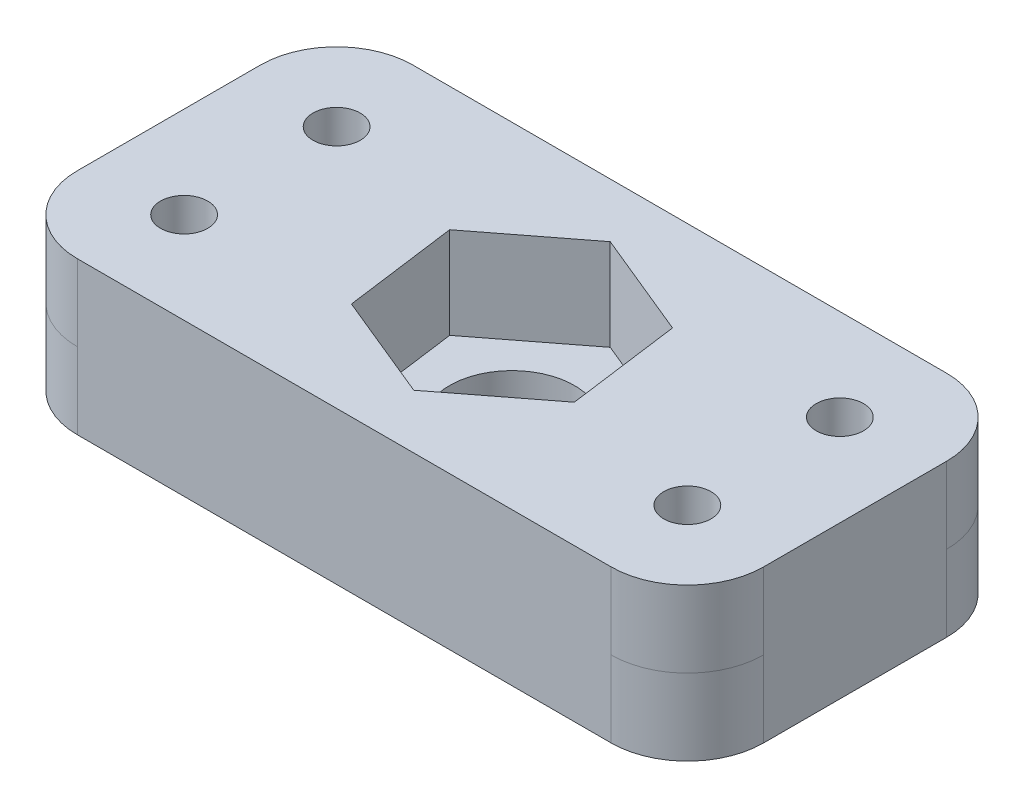
SolidWorks part; units mm, degrees
ref_plane "Alzado" through (0, 0, 0) normal (0, 0, 1) x (1, 0, 0)
ref_plane "Planta" through (0, 0, 0) normal (0, 1, 0) x (1, 0, 0)
ref_plane "Vista lateral" through (0, 0, 0) normal (1, 0, 0) x (0, 0, -1)
sketch "Croquis1" plane through (0, 0, 0) normal (0, 1, 0) x (1, 0, 0)
  circle A0 centre (0, 0) radius 10
  circle A1 centre (0, 0) radius 3.5
  dimension "D1" = 20
  dimension "D2" = 7
extrude "Extruir1" add sketch "Croquis1" along normal blind 12
sketch "Croquis2" plane through (0, 12, 0) normal (0, 1, 0) x (1, 0, 0)
  line L1 (22.5, 11) -> (-22.5, 11)
  line L2 (22.5, 11) -> (22.5, -11)
  line L3 (22.5, -11) -> (-22.5, -11)
  line L4 (-22.5, 11) -> (-22.5, -11)
  line L5 (22.5, 11) -> (-22.5, -11) construction
  line L6 (22.5, -11) -> (-22.5, 11) construction
  point P0 (0, 0)
  dimension "D1" = 45
  dimension "D2" = 22
extrude "Saliente-Extruir1" add sketch "Croquis2" along normal blind 5
fillet "Redondeo1" radius 5 1 edges at (22.5, 14.5, -11)
fillet "Redondeo2" radius 5 1 edges at (22.5, 14.5, 11)
fillet "Redondeo3" radius 5 1 edges at (-22.5, 14.5, 11)
fillet "Redondeo4" radius 5 1 edges at (-22.5, 14.5, -11)
sketch "Croquis3" plane through (0, 0, 0) normal (0, -1, 0) x (1, 0, 0)
  circle A0 centre (0, 0) radius 4.1
  dimension "D1" = 8.2
extrude "Cortar-Extruir1" cut sketch "Croquis3" against normal blind 45
sketch "Croquis4" plane through (0, 12, 0) normal (0, -1, 0) x (1, 0, 0)
  circle A0 centre (-16.5, 5) radius 1.55
  circle A1 centre (-16.5, -5) radius 1.55
  circle A2 centre (16.5, 5) radius 1.55
  circle A3 centre (16.5, -5) radius 1.55
extrude "Cortar-Extruir2" cut sketch "Croquis4" against normal blind 45
sketch "Croquis7" plane through (0, 0, 11) normal (0, 0, 1) x (1, 0, 0)
  line L0 (-17.5, 12) -> (17.5, 12) construction
  line L1 (11.057, -12) -> (-11.057, -12)
  line L2 (11.057, -12) -> (11.057, 12)
  line L3 (11.057, 12) -> (-11.057, 12)
  line L4 (-11.057, -12) -> (-11.057, 12)
  line L5 (11.057, -12) -> (-11.057, 12) construction
  line L6 (11.057, 12) -> (-11.057, -12) construction
  point P0 (0, 0)
extrude "Cortar-Extruir4" cut sketch "Croquis7" against normal blind 70
sketch "Croquis8" plane through (0, 12, 0) normal (0, -1, 0) x (1, 0, 0)
  line L1 (22.5, 11) -> (-22.5, 11)
  line L2 (22.5, 11) -> (22.5, -11)
  line L3 (22.5, -11) -> (-22.5, -11)
  line L4 (-22.5, 11) -> (-22.5, -11)
  line L5 (22.5, 11) -> (-22.5, -11) construction
  line L6 (22.5, -11) -> (-22.5, 11) construction
  point P0 (0, 0)
  dimension "D1" = 22
extrude "Saliente-Extruir2" add sketch "Croquis8" along normal blind 5
fillet "Redondeo5" radius 5 1 edges at (-22.5, 9.5, -11)
fillet "Redondeo6" radius 5 1 edges at (22.5, 9.5, -11)
fillet "Redondeo7" radius 5 1 edges at (22.5, 9.5, 11)
fillet "Redondeo8" radius 5 1 edges at (-22.5, 9.5, 11)
sketch "Croquis9" plane through (0, 17, 0) normal (0, 1, 0) x (1, 0, 0)
  circle A0 centre (-16.5, -5) radius 1.55
  circle A1 centre (-16.5, 5) radius 1.55
  circle A2 centre (16.5, -5) radius 1.55
  circle A3 centre (16.5, 5) radius 1.55
  circle A4 centre (0, 0) radius 4.1
extrude "Cortar-Extruir5" cut sketch "Croquis9" against normal blind 15
sketch "Croquis10" plane through (0, 17, 0) normal (0, 1, 0) x (1, 0, 0)
  line L1 (6.9412, -2.8553) -> (5.9434, 4.5836)
  line L2 (5.9434, 4.5836) -> (-0.9978, 7.4389)
  line L3 (-0.9978, 7.4389) -> (-6.9412, 2.8553)
  line L4 (-6.9412, 2.8553) -> (-5.9434, -4.5836)
  line L5 (-5.9434, -4.5836) -> (0.9978, -7.4389)
  line L6 (0.9978, -7.4389) -> (6.9412, -2.8553)
  circle A0 centre (0, 0) radius 6.5 construction
  dimension "D1" = 13
extrude "Cortar-Extruir7" cut sketch "Croquis10" against normal blind 6
